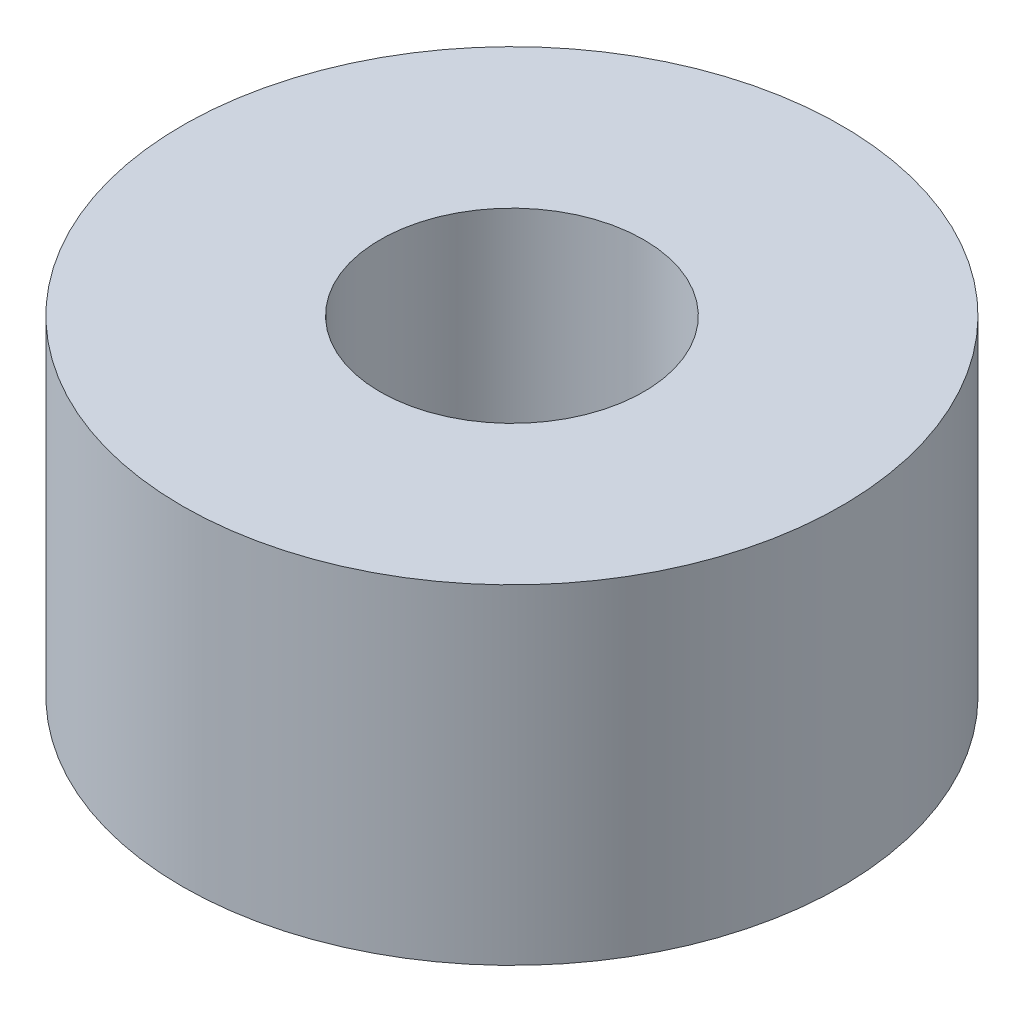
SolidWorks part; units mm, degrees
ref_plane "前视基准面" through (0, 0, 0) normal (0, 0, 1) x (1, 0, 0)
ref_plane "上视基准面" through (0, 0, 0) normal (0, 1, 0) x (1, 0, 0)
ref_plane "右视基准面" through (0, 0, 0) normal (1, 0, 0) x (0, 0, -1)
sketch "草图1" plane through (0, 0, 0) normal (0, 1, 0) x (1, 0, 0)
  circle A0 centre (0, 0) radius 2.5
  circle A1 centre (0, 0) radius 1
extrude "凸台-拉伸1" add sketch "草图1" along normal blind 2.5
